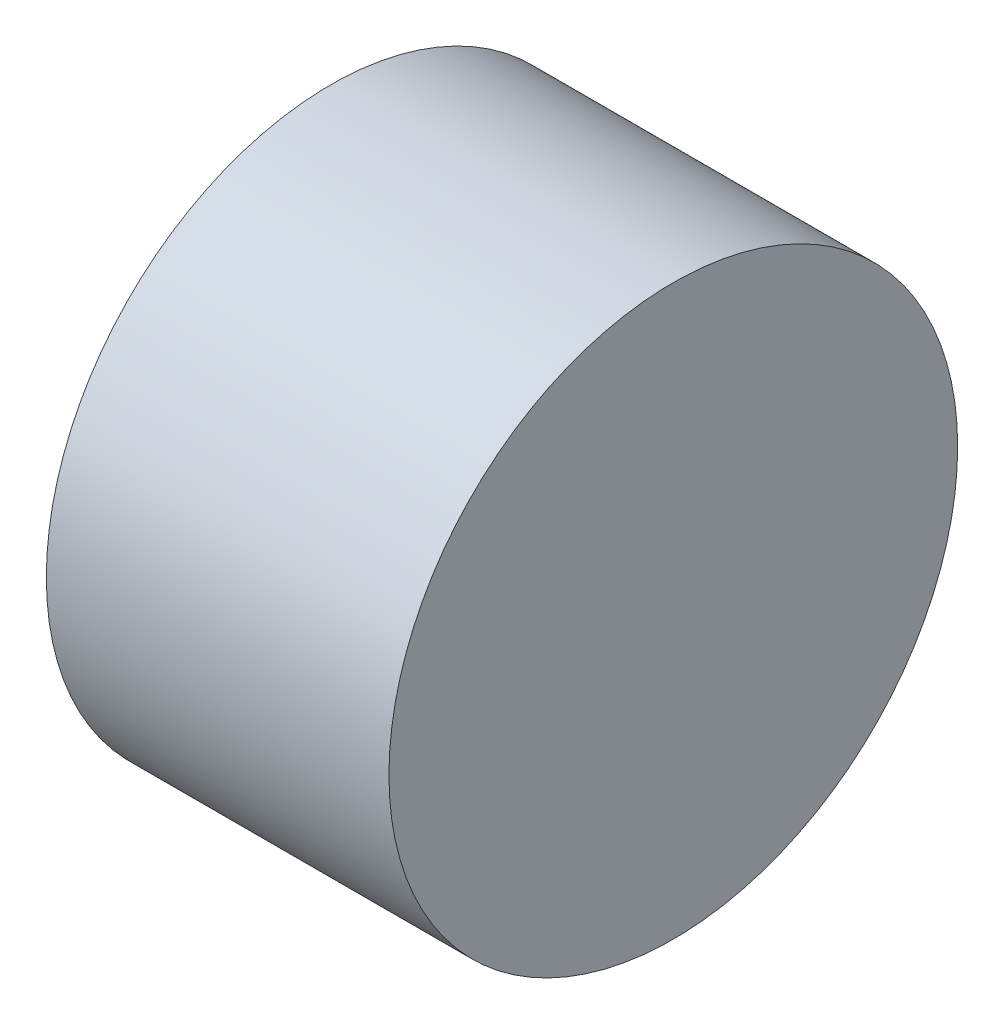
SolidWorks part; units mm, degrees
ref_plane "Front Plane" through (0, 0, 0) normal (0, 0, 1) x (1, 0, 0)
ref_plane "Top Plane" through (0, 0, 0) normal (0, 1, 0) x (1, 0, 0)
ref_plane "Right Plane" through (0, 0, 0) normal (1, 0, 0) x (0, 0, -1)
sketch "Sketch1" plane through (0, 0, 0) normal (0, 0, 1) x (1, 0, 0)
  line L0 (0, 47.4066) -> (0, -39.1523) construction
  line L1 (-29.671, 0) -> (55.9956, 0) construction
  line L3 (0, 0) -> (25.4, 0)
  line L4 (0, 0) -> (0, 21.082)
  line L5 (0, 21.082) -> (25.4, 21.082)
  line L6 (25.4, 0) -> (25.4, 21.082)
  dimension "D1" = 42.164
  dimension "D2" = 25.4
revolve "Revolve1" add sketch "Sketch1" angle 360 about L1
sketch "Sketch2" plane through (0, 0, 0) normal (-1, 0, 0) x (0, 0, 1)
  circle A0 centre (0, 0) radius 11.1125 construction
  circle A1 centre (0, 11.1125) radius 1.9844
  circle A2 centre (11.1125, 0) radius 1.9844
  circle A3 centre (0, -11.1125) radius 1.9844
  circle A4 centre (-11.1125, 0) radius 1.9844
  point P14 (0, 0)
  dimension "D1" = 22.225
  dimension "D2" = 3.9688
  dimension "D3" = 4
extrude "Cut-Extrude1" cut sketch "Sketch2" against normal blind 6.35
